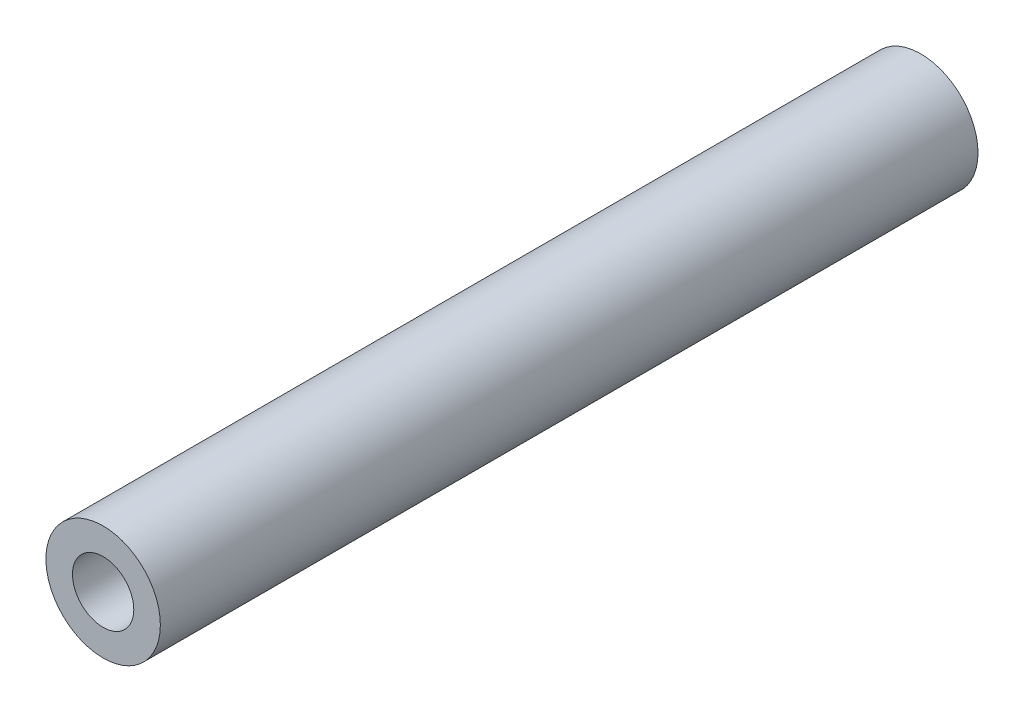
SolidWorks part; units mm, degrees
ref_plane "Piano frontale" through (0, 0, 0) normal (0, 0, 1) x (1, 0, 0)
ref_plane "Piano superiore" through (0, 0, 0) normal (0, 1, 0) x (1, 0, 0)
ref_plane "Piano destro" through (0, 0, 0) normal (1, 0, 0) x (0, 0, -1)
sketch "Sketch1" plane through (0, 0, 0) normal (0, 0, 1) x (1, 0, 0)
  circle A0 centre (0, 0) radius 2.8
  circle A1 centre (0, 0) radius 1.5
  dimension "D1" = 5.6
  dimension "D2" = 3
extrude "Boss-Extrude1" add sketch "Sketch1" along normal blind 5
sketch "Sketch2" plane through (0, 0, 5) normal (0, 0, 1) x (1, 0, 0)
  circle A0 centre (0, 0) radius 2.8
  dimension "D1" = 5.6
extrude "Boss-Extrude2" add sketch "Sketch2" along normal blind 30
sketch "Sketch3" plane through (0, 0, 35) normal (0, 0, 1) x (1, 0, 0)
  circle A0 centre (0, 0) radius 2.8
  circle A1 centre (0, 0) radius 1.5
  dimension "D1" = 5.6
  dimension "D2" = 3
extrude "Boss-Extrude3" add sketch "Sketch3" along normal blind 5
